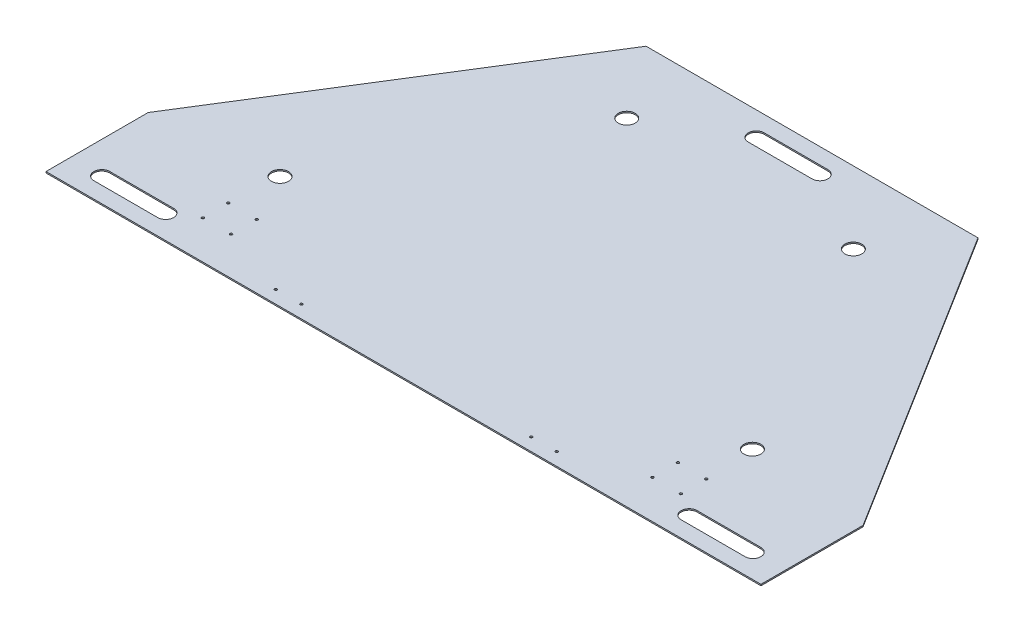
SolidWorks part; units mm, degrees
material "Alloy Steel"
ref_plane "Front Plane" through (0, 0, 0) normal (0, 0, 1) x (1, 0, 0)
ref_plane "Top Plane" through (0, 0, 0) normal (0, 1, 0) x (1, 0, 0)
ref_plane "Right Plane" through (0, 0, 0) normal (1, 0, 0) x (0, 0, -1)
sketch "Sketch1" plane through (0, 0, 0) normal (0, 1, 0) x (1, 0, 0)
  line L0 (-838.2, 0) -> (838.2, 0)
  line L1 (838.2, 0) -> (330.2, 812.8)
  line L2 (330.2, 812.8) -> (-330.2, 812.8)
  line L3 (-330.2, 812.8) -> (-838.2, 0)
  line L4 (-711.2, 203.2) -> (-711.2, 0)
  line L5 (0, 812.8) -> (0, 0) construction
  line L6 (711.2, 203.2) -> (711.2, 0)
  point P5 (0, 812.8)
  dimension "D1" = 1676.4
  dimension "D2" = 660.4
  dimension "D3" = 812.8
  dimension "D4" = 127
extrude "Boss-Extrude1" add sketch "Sketch1" along normal blind 2.6568 contours L5 L2 L3 L4 L0 | L2 L5 L0 L6 L1
sketch "Sketch2" plane through (0, 2.6568, 0) normal (0, 1, 0) x (1, 0, 0)
  line L0 (-63.5, 765.175) -> (63.5, 765.175) construction
  line L1 (-63.5, 781.05) -> (63.5, 781.05)
  line L2 (-63.5, 749.3) -> (63.5, 749.3)
  line L3 (-647.7, 47.625) -> (-520.7, 47.625) construction
  line L4 (-647.7, 63.5) -> (-520.7, 63.5)
  line L5 (-647.7, 31.75) -> (-520.7, 31.75)
  line L6 (520.7, 47.625) -> (647.7, 47.625) construction
  line L7 (520.7, 63.5) -> (647.7, 63.5)
  line L8 (520.7, 31.75) -> (647.7, 31.75)
  line L9 (0, 0) -> (0, 812.8) construction
  line L10 (330.2, 812.8) -> (-330.2, 812.8) construction
  line L11 (-711.2, 0) -> (711.2, 0) construction
  arc A0 (-63.5, 781.05) -> (-63.5, 749.3) centre (-63.5, 765.175) ccw
  arc A1 (63.5, 749.3) -> (63.5, 781.05) centre (63.5, 765.175) ccw
  arc A2 (-647.7, 63.5) -> (-647.7, 31.75) centre (-647.7, 47.625) ccw
  arc A3 (-520.7, 31.75) -> (-520.7, 63.5) centre (-520.7, 47.625) ccw
  arc A4 (520.7, 63.5) -> (520.7, 31.75) centre (520.7, 47.625) ccw
  arc A5 (647.7, 31.75) -> (647.7, 63.5) centre (647.7, 47.625) ccw
  point P2 (0, 765.175)
  point P7 (-584.2, 47.625)
  point P14 (584.2, 47.625)
  dimension "D1" = 31.75
  dimension "D2" = 31.75
  dimension "D3" = 127
  dimension "D4" = 31.75
  dimension "D5" = 31.75
  dimension "D6" = 1168.4
  dimension "D7" = 584.2
  dimension "D8" = 31.75
extrude "Cut-Extrude1" cut sketch "Sketch2" against normal through all
sketch "Sketch3" plane through (0, 2.6568, 0) normal (0, 1, 0) x (1, 0, 0)
  line L0 (-711.2, 0) -> (711.2, 0) construction
  line L1 (0, 0) -> (0, 812.8) construction
  line L2 (330.2, 812.8) -> (-330.2, 812.8) construction
  circle A0 centre (-469.9, 224.282) radius 16.891
  circle A1 centre (-225.425, 669.5864) radius 16.891
  circle A2 centre (225.425, 669.5864) radius 16.891
  circle A3 centre (469.9, 224.282) radius 16.891
  dimension "D1" = 33.782
  dimension "D3" = 469.9
  dimension "D4" = 508
  dimension "D5" = 225.425
  dimension "D2" = 224.282
extrude "Cut-Extrude2" cut sketch "Sketch3" against normal through all
hole_wizard "#10 (0.1935) Diameter Hole1" positions "Sketch4" profile "Sketch5" hole size "#10" standard "ANSI Inch" end condition through all
sketch "Sketch4" plane through (0, 2.6568, 0) normal (0, 1, 0) x (1, 0, 0)
  line L0 (-711.2, 0) -> (711.2, 0) construction
  line L1 (0, 0) -> (0, 812.8)
  line L2 (330.2, 812.8) -> (-330.2, 812.8) construction
  point P0 (228.6, 25.4)
  point P2 (279.4, 25.4)
  point P4 (419.1, 76.2)
  point P6 (419.1, 127)
  point P8 (475.488, 76.2)
  point P10 (475.488, 127)
  point P30 (-475.488, 127)
  point P31 (-475.488, 76.2)
  point P32 (-419.1, 76.2)
  point P33 (-419.1, 127)
  point P34 (-279.4, 25.4)
  point P35 (-228.6, 25.4)
  dimension "D1" = 228.6
  dimension "D2" = 50.8
  dimension "D3" = 25.4
  dimension "D4" = 76.2
  dimension "D5" = 56.388
  dimension "D6" = 419.1
  dimension "D7" = 50.8
sketch "Sketch5" plane through (228.6, 2.6568, -25.4) normal (1, 0, 0) x (0, 0, 1)
  line L0 (0, 0) -> (0, 2.6568)
  line L1 (0, 2.6568) -> (2.4574, 2.6568)
  line L2 (2.4574, 2.6568) -> (2.4574, 0)
  line L5 (2.4574, 0) -> (0, 0)
  line L11 (0, -6.35) -> (0, 107.95) construction
  dimension "Thru Hole Dia." = 4.9149
  dimension "Thru Hole Depth" = 2.6568
equation "\"D7@Sketch2\"=\"D6@Sketch2\"/2"
